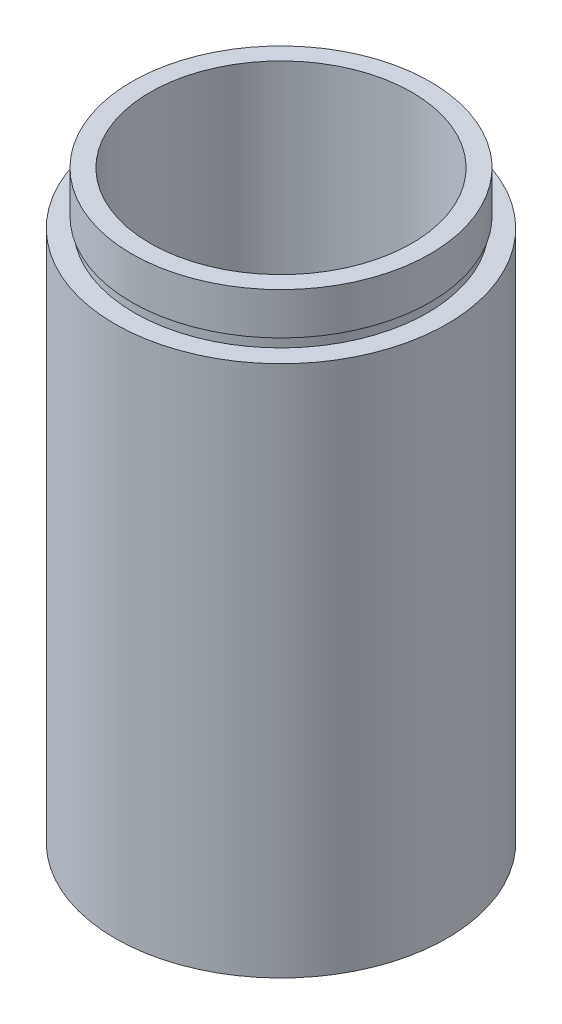
SolidWorks part; units mm, degrees
ref_plane "前视基准面" through (0, 0, 0) normal (0, 0, 1) x (1, 0, 0)
ref_plane "上视基准面" through (0, 0, 0) normal (0, 1, 0) x (1, 0, 0)
ref_plane "右视基准面" through (0, 0, 0) normal (1, 0, 0) x (0, 0, -1)
sketch "草图1" plane through (0, 0, 0) normal (0, 0, 1) x (1, 0, 0)
  line L0 (0, 161.3762) -> (0, 0) construction
  line L1 (141.7365, 0) -> (-131.7984, 0) construction
  line L2 (14.25, 0) -> (14.25, 4.5)
  line L3 (15.85, 0) -> (15.85, 50.8)
  line L4 (14.25, 0) -> (15.85, 0)
  line L5 (14.35, 4.5) -> (14.35, 5.5)
  line L6 (14.25, 4.5) -> (14.35, 4.5)
  line L7 (12.5, 5.5) -> (12.5, 55.8)
  line L8 (12.5, 5.5) -> (14.35, 5.5)
  line L9 (14.25, 55.8) -> (14.25, 51.8)
  line L10 (12.5, 55.8) -> (14.25, 55.8)
  line L11 (14, 51.8) -> (14, 50.8)
  line L12 (14, 51.8) -> (14.25, 51.8)
  line L13 (14, 50.8) -> (15.85, 50.8)
  point P7 (14.25, 2.25)
  dimension "D1" = 14.25
  dimension "D2" = 4.5
  dimension "D3" = 15.85
  dimension "D4" = 14.35
  dimension "D5" = 12.5
  dimension "D6" = 1
  dimension "D7" = 50.8
  dimension "D8" = 14.25
  dimension "D9" = 14
  dimension "D10" = 5
  dimension "D11" = 1
revolve "旋转1" add sketch "草图1" angle 360 about L0
cosmetic thread "装饰螺纹线1" parameters "D2"=28.51
cosmetic thread "装饰螺纹线2" parameters "D2"=26
cosmetic thread "装饰螺纹线3" parameters "D2"=28.49
